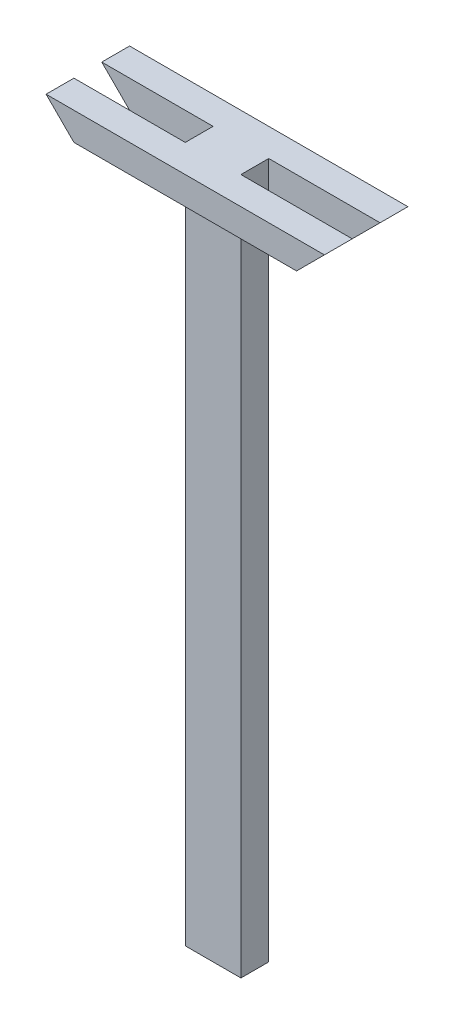
SolidWorks part; units mm, degrees
ref_plane "前视基准面" through (0, 0, 0) normal (0, 0, 1) x (1, 0, 0)
ref_plane "上视基准面" through (0, 0, 0) normal (0, 1, 0) x (1, 0, 0)
ref_plane "右视基准面" through (0, 0, 0) normal (1, 0, 0) x (0, 0, -1)
sketch "草图1" plane through (0, 0, 0) normal (0, 1, 0) x (1, 0, 0)
  line L1 (0, 0) -> (80, 0)
  line L2 (0, 0) -> (0, -40)
  line L3 (0, -40) -> (80, -40)
  line L4 (80, 0) -> (80, -40)
  dimension "D1" = 40
  dimension "D2" = 80
extrude "凸台-拉伸1" add sketch "草图1" along normal blind 1000
sketch "草图2" plane through (0, 0, 40) normal (0, 0, 1) x (1, 0, 0)
  line L0 (40, 1000) -> (40, 0) construction
  line L1 (-160, 1000) -> (240, 1000)
  line L2 (-160, 1000) -> (-160, 960)
  line L3 (-160, 960) -> (240, 960)
  line L4 (240, 1000) -> (240, 960)
  line L5 (0, 1000) -> (80, 1000) construction
  line L6 (0, 0) -> (80, 0) construction
  dimension "D1" = 40
  dimension "D2" = 200
  dimension "D3" = 200
extrude "凸台-拉伸2" add sketch "草图2" along normal blind 40
sketch "草图3" plane through (0, 0, 0) normal (0, 0, -1) x (-1, 0, 0)
  line L0 (-40, 1000) -> (-40, 0) construction
  line L1 (-80, 1000) -> (0, 1000) construction
  line L2 (-80, 0) -> (0, 0) construction
  line L8 (-240, 1000) -> (160, 1000)
  line L9 (-240, 1000) -> (-240, 960)
  line L10 (-240, 960) -> (160, 960)
  line L11 (160, 1000) -> (160, 960)
  dimension "D1" = 200
  dimension "D2" = 200
  dimension "D3" = 40
extrude "凸台-拉伸3" add sketch "草图3" along normal blind 40
sketch "草图4" plane through (0, 0, 80) normal (0, 0, 1) x (1, 0, 0)
  line L0 (-160, 1000) -> (-120, 960)
  line L1 (240, 1000) -> (200, 960)
  line L3 (-160, 960) -> (240, 960) construction
  line L4 (-160, 1000) -> (-160, 960)
  line L5 (-160, 960) -> (240, 960)
  line L6 (240, 960) -> (240, 1000)
  line L7 (240, 1000) -> (-160, 1000)
  line L8 (-160, 1000) -> (-160, 960)
  line L9 (-160, 960) -> (-120, 960)
  line L10 (240, 960) -> (240, 1000)
  line L12 (200, 960) -> (240, 960)
  dimension "D2" = 45
  dimension "D3" = 45
  dimension "D1" = 0
extrude "切除-拉伸1" cut sketch "草图4" against normal through all
